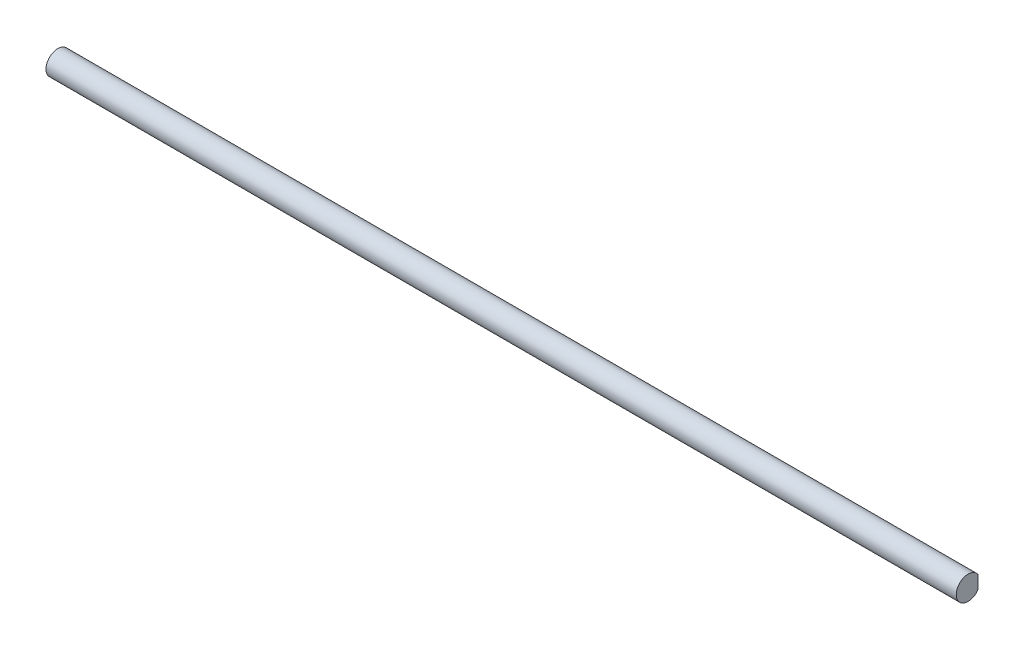
SolidWorks part; units mm, degrees
ref_plane "前视基准面" through (0, 0, 0) normal (0, 0, 1) x (1, 0, 0)
ref_plane "上视基准面" through (0, 0, 0) normal (0, 1, 0) x (1, 0, 0)
ref_plane "右视基准面" through (0, 0, 0) normal (1, 0, 0) x (0, 0, -1)
other "Configuration Table"
sketch "草图1" plane through (0, 0, 0) normal (1, 0, 0) x (0, 0, -1)
  circle A0 centre (0, 0) radius 6
  dimension "D1" = 12
extrude "凸台-拉伸1" add sketch "草图1" along normal blind 460
sketch "草图2" plane through (0, 0, 0) normal (0, 1, 0) x (1, 0, 0)
  line L0 (0, 6) -> (15.5, 6)
  line L1 (460, 6) -> (0, 6) construction
  line L2 (15.5, 6) -> (15.5, 5)
  line L3 (15.5, 5) -> (0, 5)
  line L4 (0, 6) -> (0, -6) construction
  line L5 (0, 5) -> (0, 6)
  dimension "D1" = 15.5
  dimension "D2" = 1
extrude "切除-拉伸1" cut sketch "草图2" against normal mid plane 400
ref_plane "基准面1" through (230, 0, 0) normal (-1, 0, 0) x (0, 0, 1)
mirror "镜向1" about plane through (230, 0, 0) normal (-1, 0, 0) of "切除-拉伸1"
